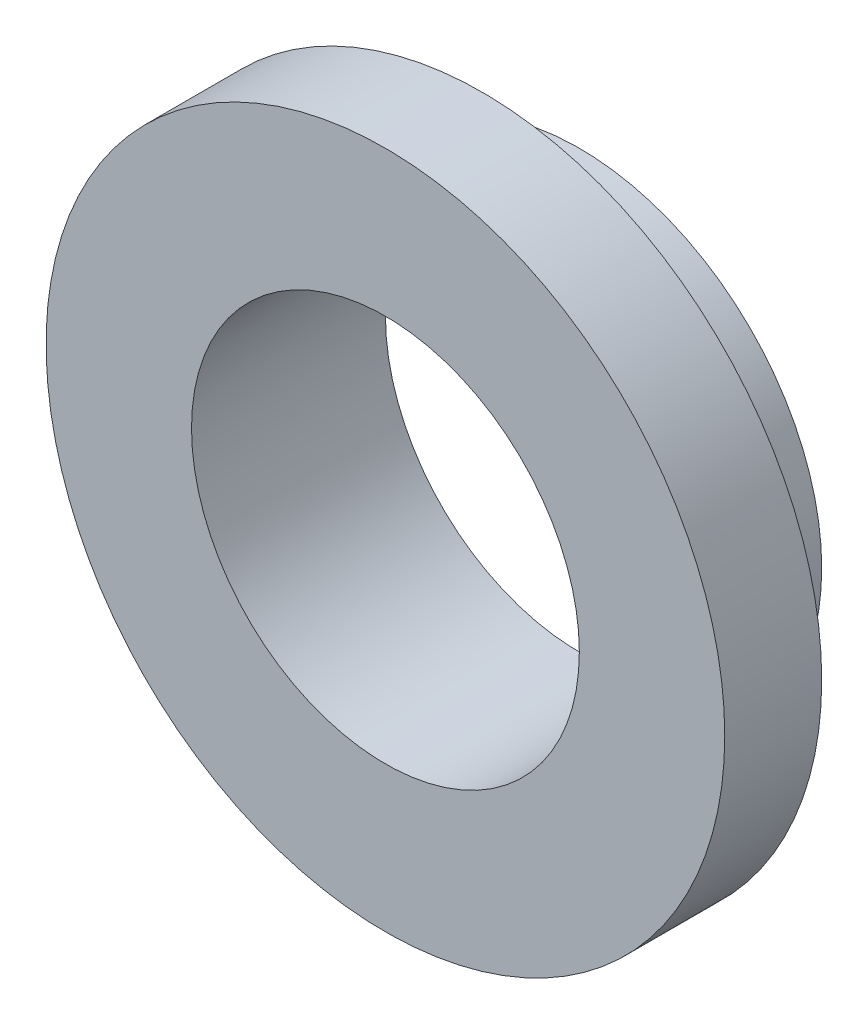
SolidWorks part; units mm, degrees
material "2014-T6"
ref_plane "Ebene vorne" through (0, 0, 0) normal (0, 0, 1) x (1, 0, 0)
ref_plane "Ebene oben" through (0, 0, 0) normal (0, 1, 0) x (1, 0, 0)
ref_plane "Ebene rechts" through (0, 0, 0) normal (1, 0, 0) x (0, 0, -1)
sketch "Skizze1" plane through (0, 0, 0) normal (0, 0, 1) x (1, 0, 0)
  circle A0 centre (0, 0) radius 2
  circle A1 centre (0, 0) radius 2.5
  dimension "D1" = 4
  dimension "D2" = 5
extrude "Aufsatz-Linear austragen1" add sketch "Skizze1" along normal mid plane 2
sketch "Skizze2" plane through (0, 0, 1) normal (0, 0, 1) x (1, 0, 0)
  circle A0 centre (0, 0) radius 3.5
  circle A1 centre (0, 0) radius 2 construction
  circle A2 centre (0, 0) radius 2
  dimension "D1" = 7
extrude "Aufsatz-Linear austragen2" add sketch "Skizze2" against normal blind 1
